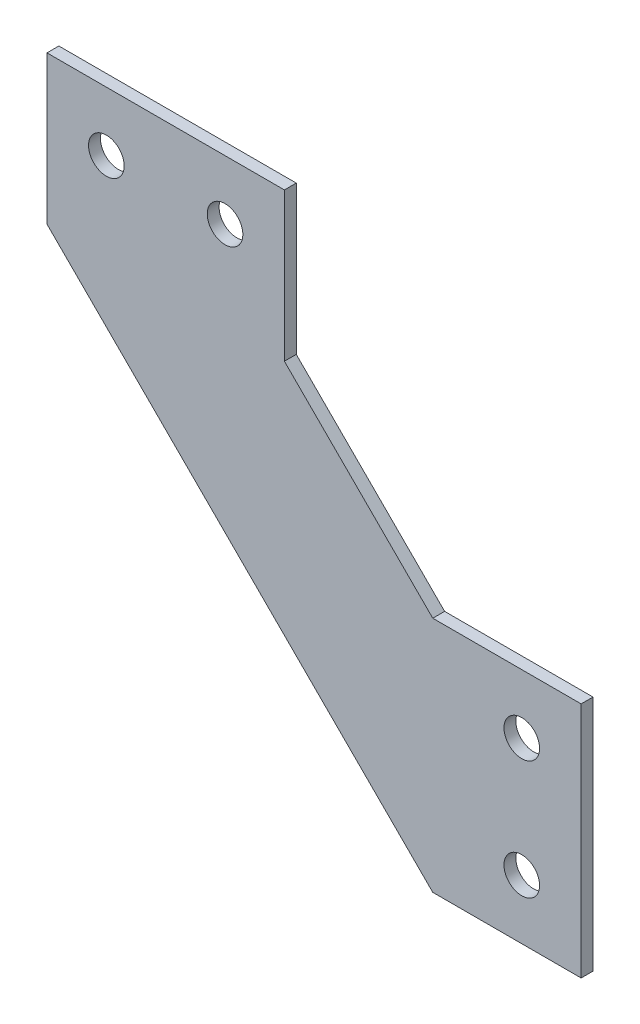
SolidWorks part; units mm, degrees
ref_plane "Front Plane" through (0, 0, 0) normal (0, 0, 1) x (1, 0, 0)
ref_plane "Top Plane" through (0, 0, 0) normal (0, 1, 0) x (1, 0, 0)
ref_plane "Right Plane" through (0, 0, 0) normal (1, 0, 0) x (0, 0, -1)
ref_plane "Plane1" through (0, 0, 59.2994) normal (0, 0, -1) x (-1, 0, 0)
sketch "Sketch1" plane through (0, 0, 59.2994) normal (0, 0, -1) x (-1, 0, 0)
  line L0 (122.0351, 44.5501) -> (122.0351, -43.4499) construction
  line L1 (142.0351, 64.5501) -> (230.0351, 64.5501) construction
  line L2 (122.0351, 64.5501) -> (122.0351, 14.5501) construction
  line L3 (122.0351, 64.5501) -> (172.0351, 64.5501) construction
  line L4 (212.0351, 44.5501) -> (212.0351, 39.5501)
  line L5 (122.2351, 44.5501) -> (127.3851, 44.5501) construction
  line L6 (122.0351, -25.4499) -> (142.0351, -25.4499)
  line L7 (122.0351, -25.4499) -> (122.0351, 14.5501)
  line L8 (122.0351, 14.5501) -> (142.0351, 14.5501)
  line L9 (212.0351, 64.5501) -> (172.0351, 64.5501)
  line L10 (212.0351, 64.5501) -> (212.0351, 44.5501)
  line L11 (172.0351, 64.5501) -> (172.0351, 44.5501)
  line L14 (132.0351, -25.4499) -> (132.0351, 14.5501) construction
  line L15 (172.0351, 54.5501) -> (212.0351, 54.5501) construction
  line L18 (142.0351, 59.2001) -> (142.0351, 64.3501) construction
  line L19 (142.0351, 14.5501) -> (172.0351, 44.5501) construction
  line L20 (142.0351, -25.4499) -> (212.0351, 44.5501) construction
  line L21 (142.0351, -25.4499) -> (147.0351, -25.4499)
  line L22 (212.0351, 39.5501) -> (147.0351, -25.4499)
  line L23 (172.0351, 44.5501) -> (172.0351, 39.5501)
  line L24 (172.0351, 39.5501) -> (147.0351, 14.5501)
  line L25 (147.0351, 14.5501) -> (142.0351, 14.5501)
  circle A0 centre (202.0351, 54.5501) radius 3
  circle A1 centre (182.0351, 54.5501) radius 3
  circle A2 centre (132.0351, -15.4499) radius 3
  circle A3 centre (132.0351, 4.5501) radius 3
  dimension "D4" = 6
  dimension "D7" = 6
  dimension "D8" = 6
  dimension "D9" = 6
  dimension "D1" = 40
  dimension "D2" = 40
  dimension "D3" = 30
  dimension "D5" = 10
  dimension "D6" = 10
  dimension "D10" = 10
  dimension "D11" = 10
  dimension "D12" = 20
  dimension "D13" = 20
  dimension "D14" = 30
  dimension "D15" = 5
extrude "Boss-Extrude1" add sketch "Sketch1" along normal blind 2
